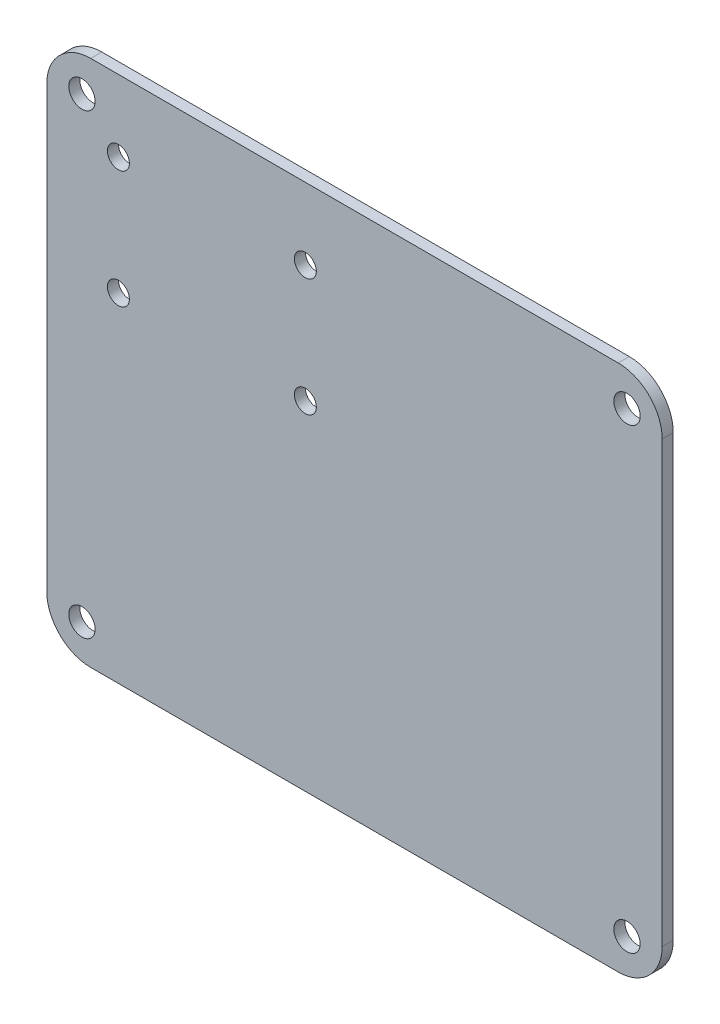
SolidWorks part; units mm, degrees
ref_plane "Front Plane" through (0, 0, 0) normal (0, 0, 1) x (1, 0, 0)
ref_plane "Top Plane" through (0, 0, 0) normal (0, 1, 0) x (1, 0, 0)
ref_plane "Right Plane" through (0, 0, 0) normal (1, 0, 0) x (0, 0, -1)
sketch "Sketch1" plane through (0, 0, 0) normal (0, 0, 1) x (1, 0, 0)
  line L1 (-15.4905, -8.0369) -> (73.4095, -8.0369)
  line L2 (-15.4905, -8.0369) -> (-15.4905, 68.1631)
  line L3 (-15.4905, 68.1631) -> (73.4095, 68.1631)
  line L4 (73.4095, -8.0369) -> (73.4095, 68.1631)
  line L8 (25.8595, 61.8131) -> (-9.1405, 61.8131) construction
  line L9 (-9.1405, 61.8131) -> (-9.1405, 36.8131) construction
  dimension "D1" = 76.2
  dimension "D2" = 88.9
  dimension "D3" = 6.35
  dimension "D4" = 6.35
extrude "Boss-Extrude1" add sketch "Sketch1" along normal blind 1.6
sketch "Sketch2" plane through (0, 0, 0) normal (0, 0, -1) x (-1, 0, 0)
  circle A0 centre (5.1405, 57.8131) radius 1.5875 construction
  circle A1 centre (-21.8595, 57.8131) radius 1.5875 construction
  circle A2 centre (-21.8595, 40.8131) radius 1.5875 construction
  circle A3 centre (5.1405, 40.8131) radius 1.5875 construction
  circle A4 centre (5.1405, 57.8131) radius 1.5875
  circle A5 centre (-21.8595, 57.8131) radius 1.5875
  circle A6 centre (-21.8595, 40.8131) radius 1.5875
  circle A7 centre (5.1405, 40.8131) radius 1.5875
extrude "Cut-Extrude1" cut sketch "Sketch2" against normal through all
sketch "Sketch4" plane through (0, 0, 0) normal (0, 0, -1) x (-1, 0, 0)
  line L0 (-28.9595, 68.1631) -> (-28.9595, -8.0369) construction
  line L1 (-73.4095, 68.1631) -> (15.4905, 68.1631) construction
  line L2 (15.4905, -8.0369) -> (-73.4095, -8.0369) construction
  line L3 (-73.4095, 30.0631) -> (15.4905, 30.0631) construction
  line L4 (-73.4095, -8.0369) -> (-73.4095, 68.1631) construction
  line L5 (15.4905, 68.1631) -> (15.4905, -8.0369) construction
  circle A0 centre (10.4105, 63.0831) radius 1.905
  circle A1 centre (-68.3295, 63.0831) radius 1.905
  circle A2 centre (-68.3295, -2.9569) radius 1.905
  circle A3 centre (10.4105, -2.9569) radius 1.905
  dimension "D1" = 3.81
  dimension "D2" = 5.08
  dimension "D3" = 5.08
extrude "Cut-Extrude2" cut sketch "Sketch4" against normal through all
fillet "Fillet1" radius 6.35 4 edges at (73.4095, 68.1631, 0.8) (73.4095, -8.0369, 0.8) (-15.4905, -8.0369, 0.8) (-15.4905, 68.1631, 0.8)
sketch "Sketch5" plane through (0, 0, 1.6) normal (0, 0, 1) x (1, 0, 0)
  line L0 (-15.4905, 61.8131) -> (-15.4905, -1.6869) construction
  line L1 (-9.1405, -8.0369) -> (67.0595, -8.0369) construction
  line L2 (67.0595, 68.1631) -> (-9.1405, 68.1631) construction
  line L7 (-9.1405, 61.8131) -> (-9.1405, 36.8131)
  line L8 (-9.1405, 36.8131) -> (25.8595, 36.8131)
  line L9 (25.8595, 36.8131) -> (25.8595, 61.8131)
  line L10 (25.8595, 61.8131) -> (-9.1405, 61.8131)
  line L11 (-9.1405, 61.8131) -> (-9.1405, 36.8131)
  line L12 (-9.1405, 36.8131) -> (25.8595, 36.8131)
  line L13 (25.8595, 36.8131) -> (25.8595, 61.8131)
  line L14 (25.8595, 61.8131) -> (-9.1405, 61.8131)
  circle A0 centre (-10.4105, -2.9569) radius 1.905 construction
  circle A1 centre (-5.1405, 40.8131) radius 1.5875 construction
  circle A2 centre (-5.1405, 40.8131) radius 1.5875
  circle A3 centre (-10.4105, -2.9569) radius 1.905
  circle A4 centre (15.8595, 42.8131) radius 3 construction
  circle A5 centre (1.8595, 49.3131) radius 2.3812
  circle A6 centre (1.8595, 49.3131) radius 2.3812
  circle A7 centre (15.8595, 55.8131) radius 3 construction
  circle A8 centre (15.8595, 42.8131) radius 3
  circle A9 centre (15.8595, 55.8131) radius 3
  point P0 (-10.4105, 63.0831)
  point P1 (-10.4105, -2.9569)
  point P3 (68.3295, -2.9569)
  point P5 (68.3295, 63.0831)
  point P7 (-5.1405, 57.8131)
  point P9 (-5.1405, 40.8131)
  point P11 (21.8595, 40.8131)
  point P13 (21.8595, 57.8131)
  point P15 (-15.4905, -8.0369)
  point P30 (-15.4905, 68.1631)
  dimension "D9" = 3.175
  dimension "D10" = 3.81
  dimension "D2" = 5.08
  dimension "D3" = 10.35
  dimension "D4" = 27.35
  dimension "D5" = 71.12
  dimension "D6" = 10.35
  dimension "D7" = 37.35
  dimension "D8" = 83.82
  dimension "D12" = 31.35
  dimension "D13" = 25.35
  dimension "D14" = 12.35
  dimension "D15" = 18.85
  dimension "D16" = 17.35
  dimension "D18" = 6.35
  dimension "D19" = 6.35
  dimension "D20" = 41.35
  dimension "D21" = 31.35
  dimension "D11" = 0
  dimension "D17" = 0
ref_plane "Plane1" through (28.9595, 0, 0) normal (-1, 0, 0) x (0, 0, 1)
